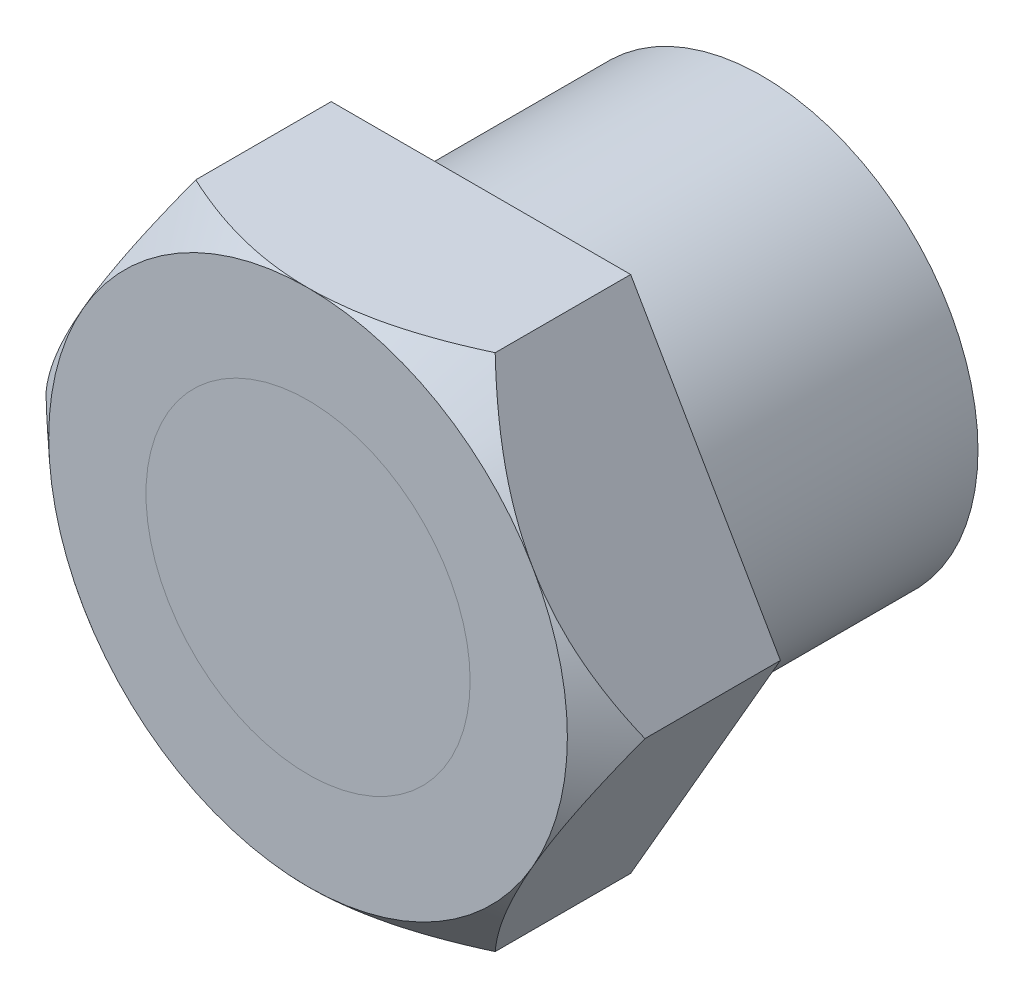
SolidWorks part; units mm, degrees
material "Lega 1060"
ref_plane "Piano frontale" through (0, 0, 0) normal (0, 0, 1) x (1, 0, 0)
ref_plane "Piano superiore" through (0, 0, 0) normal (0, 1, 0) x (1, 0, 0)
ref_plane "Piano destro" through (0, 0, 0) normal (1, 0, 0) x (0, 0, -1)
sketch "Schizzo1" plane through (0, 0, 0) normal (0, 0, 1) x (1, 0, 0)
  circle A0 centre (0, 0) radius 10
  circle A1 centre (0, 0) radius 7.5
  dimension "D1" = 20
  dimension "D2" = 15
extrude "Estrusione-Estrusione1" add sketch "Schizzo1" along normal blind 13
cosmetic thread "Filettatura cosmetica1" parameters "D2"=17.252
sketch "Schizzo2" plane through (0, 0, 13) normal (0, 0, 1) x (1, 0, 0)
  line L7 (6.9282, 12) -> (-6.9282, 12)
  line L8 (-6.9282, 12) -> (-13.8564, 0)
  line L9 (-13.8564, 0) -> (-6.9282, -12)
  line L10 (-6.9282, -12) -> (6.9282, -12)
  line L11 (6.9282, -12) -> (13.8564, 0)
  line L12 (13.8564, 0) -> (6.9282, 12)
  circle A0 centre (0, 0) radius 7.5 construction
  circle A1 centre (0, 0) radius 7.5
  circle A3 centre (0, 0) radius 12 construction
  dimension "D1" = 24
extrude "Estrusione-Estrusione2" add sketch "Schizzo2" along normal blind 8
sketch "Schizzo3" plane through (0, 0, 21) normal (0, 0, 1) x (1, 0, 0)
  circle A0 centre (0, 0) radius 12
  dimension "D1" = 24
extrude "Taglio-Estrusione1" cut sketch "Schizzo3" against normal blind 2 draft 47 flip side to cut contours A0
sketch "Schizzo4" plane through (0, 0, 21) normal (0, 0, 1) x (1, 0, 0)
  circle A0 centre (0, 0) radius 7.5 construction
  circle A1 centre (0, 0) radius 7.5
extrude "Estrusione-Estrusione3" add sketch "Schizzo4" against normal blind 3 separate body
fillet "Raccordo1" [suppressed] radius 0.5
